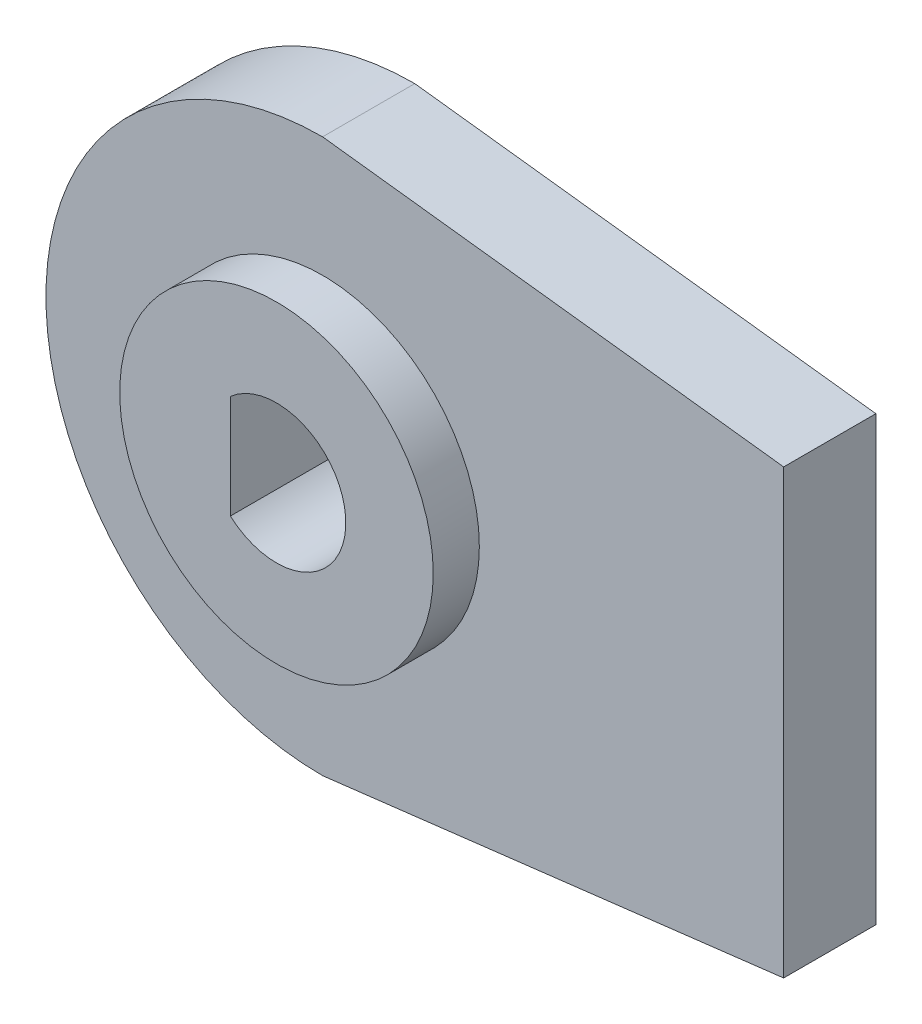
SolidWorks part; units mm, degrees
ref_plane "Front Plane" through (0, 0, 0) normal (0, 0, 1) x (1, 0, 0)
ref_plane "Top Plane" through (0, 0, 0) normal (0, 1, 0) x (1, 0, 0)
ref_plane "Right Plane" through (0, 0, 0) normal (1, 0, 0) x (0, 0, -1)
sketch "Sketch2" plane through (0, 0, 0) normal (0, 0, 1) x (1, 0, 0)
  line L2 (10, -4.8) -> (10, 4.8)
  line L3 (0, 6) -> (10, 4.8)
  line L4 (0, -6) -> (10, -4.8)
  arc A0 (0, 6) -> (0, -6) centre (0, 0) ccw
  point P1 (10, 0)
  dimension "D1" = 12
  dimension "D2" = 10
  dimension "D3" = 9.6
  dimension "D4" = 0
extrude "Boss-Extrude1" add sketch "Sketch2" along normal blind 2
sketch "Sketch7" plane through (0, 0, 2) normal (0, 0, 1) x (1, 0, 0)
  circle A0 centre (0, 0) radius 3.4
  dimension "D1" = 6.8
extrude "Boss-Extrude2" add sketch "Sketch7" along normal blind 1
sketch "Sketch8" plane through (0, 0, 3) normal (0, 0, 1) x (1, 0, 0)
  line L0 (-1, 1.1229) -> (-1, -1.1229)
  arc A1 (-1, -1.1229) -> (-1, 1.1229) centre (0, 0) ccw
  dimension "D1" = 1
extrude "Cut-Extrude3" cut sketch "Sketch8" against normal through all contours A1 L0
